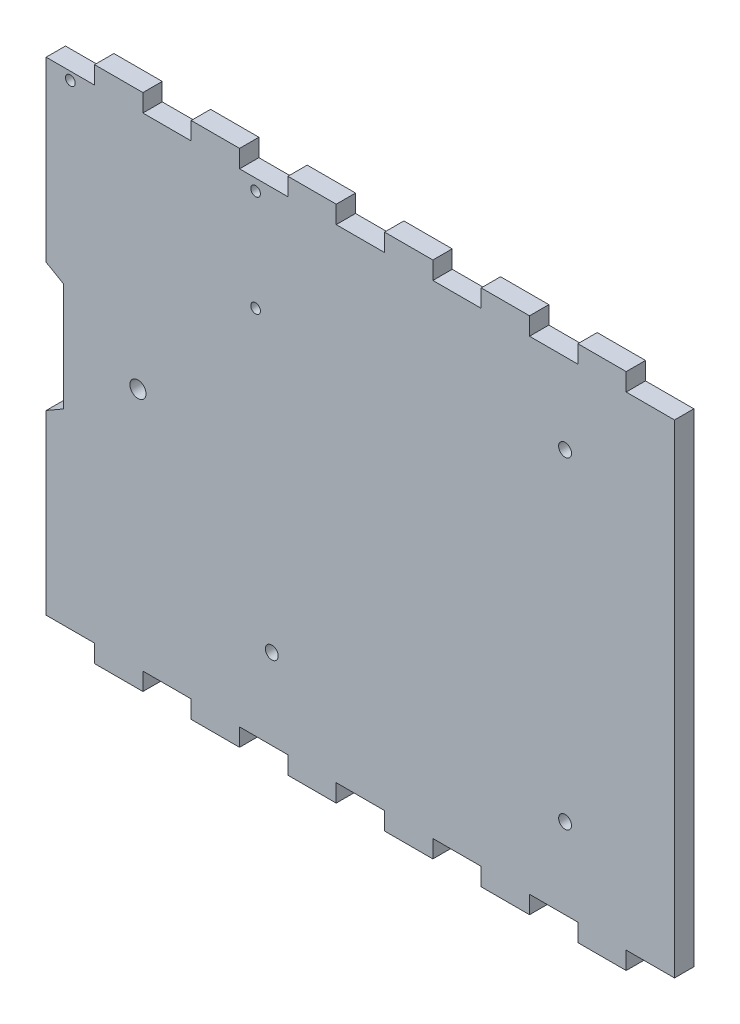
SolidWorks part; units mm, degrees
ref_plane "Front Plane" through (0, 0, 0) normal (0, 0, 1) x (1, 0, 0)
ref_plane "Top Plane" through (0, 0, 0) normal (0, 1, 0) x (1, 0, 0)
ref_plane "Right Plane" through (0, 0, 0) normal (1, 0, 0) x (0, 0, -1)
sketch "Model" plane through (0, 0, 0) normal (0, 0, 1) x (1, 0, 0)
  line L0 (206.6991, 163.4372) -> (206.6991, 13.4372)
  line L1 (191.6991, 7.9372) -> (176.6991, 7.9372)
  line L2 (161.6991, 7.9372) -> (146.6991, 7.9372)
  line L3 (131.6991, 7.9372) -> (116.6991, 7.9372)
  line L4 (101.6991, 7.9372) -> (86.6991, 7.9372)
  line L5 (71.6991, 7.9372) -> (56.6991, 7.9372)
  line L6 (41.6991, 7.9372) -> (26.6991, 7.9372)
  line L7 (11.669, 13.4372) -> (26.6991, 13.4372)
  line L8 (26.6991, 13.4372) -> (26.6991, 7.9372)
  line L9 (41.6991, 13.4372) -> (56.6991, 13.4372)
  line L10 (71.6991, 13.4372) -> (86.6991, 13.4372)
  line L11 (101.6991, 13.4372) -> (116.6991, 13.4372)
  line L12 (131.6991, 13.4372) -> (146.6991, 13.4372)
  line L13 (161.6991, 13.4372) -> (176.6991, 13.4372)
  line L14 (191.6991, 13.4372) -> (206.6991, 13.4372)
  line L15 (41.6991, 7.9372) -> (41.6991, 13.4372)
  line L16 (56.6991, 7.9372) -> (56.6991, 13.4372)
  line L17 (116.6991, 7.9372) -> (116.6991, 13.4372)
  line L18 (86.6991, 7.9372) -> (86.6991, 13.4372)
  line L19 (101.6991, 7.9372) -> (101.6991, 13.4372)
  line L20 (131.6991, 7.9372) -> (131.6991, 13.4372)
  line L21 (71.6991, 7.9372) -> (71.6991, 13.4372)
  line L22 (146.6991, 7.9372) -> (146.6991, 13.4372)
  line L23 (161.6991, 7.9372) -> (161.6991, 13.4372)
  line L24 (176.6991, 7.9372) -> (176.6991, 13.4372)
  line L25 (191.6991, 7.9372) -> (191.6991, 13.4372)
  line L26 (191.6991, 168.9372) -> (176.6991, 168.9372)
  line L27 (161.6991, 168.9372) -> (146.6991, 168.9372)
  line L28 (131.6991, 168.9372) -> (116.6991, 168.9372)
  line L29 (101.6991, 168.9372) -> (86.6991, 168.9372)
  line L30 (71.6991, 168.9372) -> (56.6991, 168.9372)
  line L31 (41.6991, 168.9372) -> (26.6991, 168.9372)
  line L32 (11.669, 163.4372) -> (26.6991, 163.4372)
  line L33 (26.6991, 163.4372) -> (26.6991, 168.9372)
  line L34 (41.6991, 163.4372) -> (56.6991, 163.4372)
  line L35 (71.6991, 163.4372) -> (86.6991, 163.4372)
  line L36 (101.6991, 163.4372) -> (116.6991, 163.4372)
  line L37 (131.6991, 163.4372) -> (146.6991, 163.4372)
  line L38 (161.6991, 163.4372) -> (176.6991, 163.4372)
  line L39 (191.6991, 163.4372) -> (206.6991, 163.4372)
  line L40 (41.6991, 168.9372) -> (41.6991, 163.4372)
  line L41 (56.6991, 168.9372) -> (56.6991, 163.4372)
  line L42 (116.6991, 168.9372) -> (116.6991, 163.4372)
  line L43 (86.6991, 168.9372) -> (86.6991, 163.4372)
  line L44 (101.6991, 168.9372) -> (101.6991, 163.4372)
  line L45 (131.6991, 168.9372) -> (131.6991, 163.4372)
  line L46 (71.6991, 168.9372) -> (71.6991, 163.4372)
  line L47 (146.6991, 168.9372) -> (146.6991, 163.4372)
  line L48 (161.6991, 168.9372) -> (161.6991, 163.4372)
  line L49 (176.6991, 168.9372) -> (176.6991, 163.4372)
  line L50 (191.6991, 168.9372) -> (191.6991, 163.4372)
  line L51 (11.669, 68.4693) -> (11.669, 13.4372)
  line L52 (11.669, 163.4372) -> (11.669, 108.3064)
  line L53 (11.669, 68.4693) -> (17.0086, 71.5521)
  line L54 (11.669, 108.3064) -> (17.0086, 105.2236)
  line L55 (17.0086, 71.5521) -> (17.0086, 105.2236)
  circle A0 centre (40.169, 88.4372) radius 2.5
  circle A1 centre (172.7311, 138.4372) radius 2
  circle A2 centre (81.6991, 38.4372) radius 2
  circle A3 centre (172.7311, 38.4372) radius 2
  circle A4 centre (76.669, 128.4372) radius 1.5
  circle A5 centre (76.669, 159.9372) radius 1.5
  circle A6 centre (19.184, 160.9372) radius 1.5
extrude "Boss-Extrude1" add sketch "Model" along normal blind 6 contours L52 L54 L55 L53 L51 L7 L8 L6 L15 L9 L16 L5 L21 L10 L18 L4 L19 L11 L17 L3 L20 L12 L22 L2 L23 L13 L24 L1 L25 L14 L0 L39 L50 L26 L49 L38 L48 L27 L47 L37 L45 L28 L42 L36 L44 L29 L43 L35 L46 L30 L41 L34 L40 L31 L33 L32 | A2 | A3 | A1 | A4 | A0 | A5 | A6
